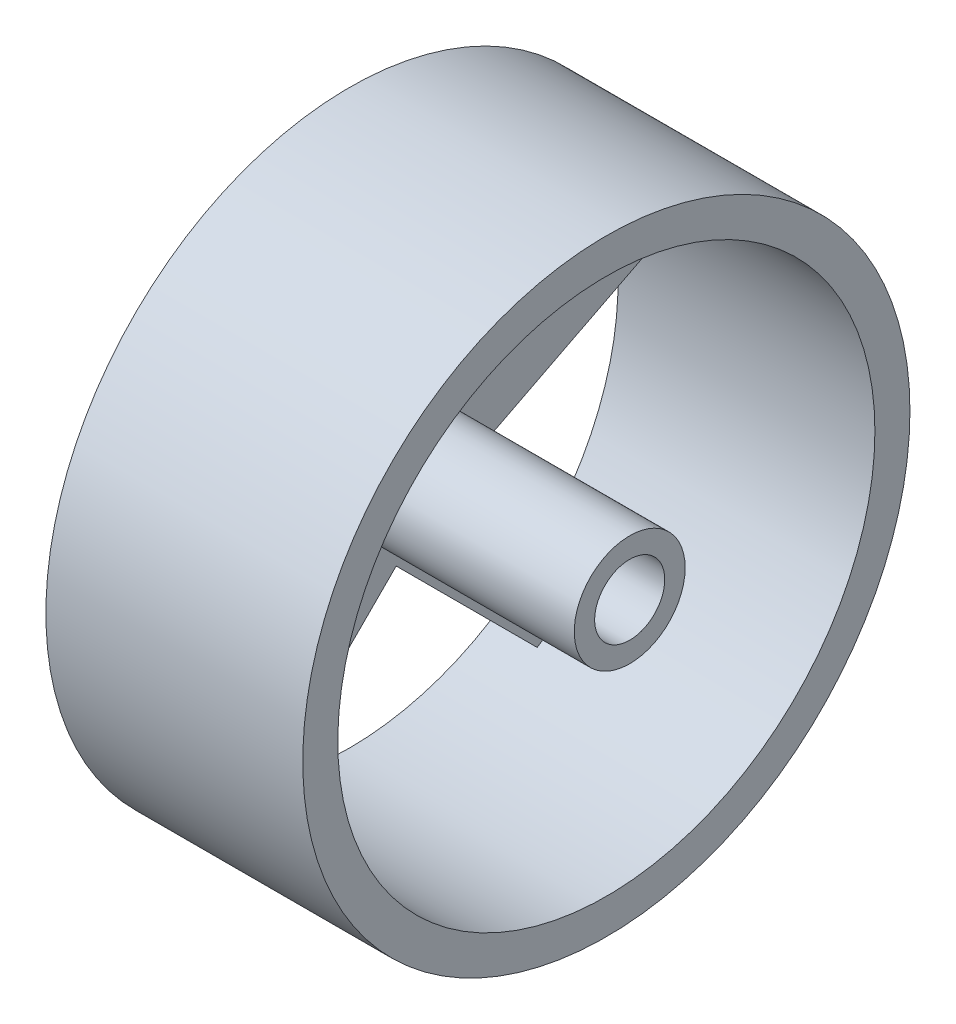
SolidWorks part; units mm, degrees
ref_plane "前视基准面" through (0, 0, 0) normal (0, 0, 1) x (1, 0, 0)
ref_plane "上视基准面" through (0, 0, 0) normal (0, 1, 0) x (1, 0, 0)
ref_plane "右视基准面" through (0, 0, 0) normal (1, 0, 0) x (0, 0, -1)
other "Configuration Table"
sketch "草图1" plane through (0, 0, 0) normal (1, 0, 0) x (0, 0, -1)
  circle A0 centre (0, 0) radius 26
  dimension "D1" = 52
extrude "凸台-拉伸1" add sketch "草图1" along normal blind 4
sketch "草图2" plane through (4, 0, 0) normal (1, 0, 0) x (0, 0, -1)
  circle A0 centre (0, 0) radius 4.75
  dimension "D1" = 9.5
extrude "凸台-拉伸2" add sketch "草图2" along normal blind 20
sketch "草图3" plane through (24, 0, 0) normal (1, 0, 0) x (0, 0, -1)
  circle A0 centre (0, 0) radius 3
  dimension "D1" = 6
extrude "切除-拉伸1" cut sketch "草图3" against normal blind 20
sketch "草图4" plane through (4, 0, 0) normal (1, 0, 0) x (0, 0, -1)
  circle A0 centre (0, 0) radius 23
  circle A1 centre (0, 0) radius 26 construction
  circle A2 centre (0, 0) radius 26
  dimension "D1" = 3
extrude "凸台-拉伸3" add sketch "草图4" along normal blind 18
sketch "草图5" plane through (4, 0, 0) normal (1, 0, 0) x (0, 0, -1)
  line L0 (0, 0) -> (-13.5191, 18.6074) construction
  line L1 (-21.2751, 8.739) -> (-4.4084, 6.0676)
  line L2 (-1.737, 22.9343) -> (-4.4084, 6.0676)
  line L3 (21.2751, 8.739) -> (4.4084, 6.0676)
  line L4 (1.737, 22.9343) -> (4.4084, 6.0676)
  line L5 (14.8857, -17.5333) -> (7.1329, -2.3176)
  line L6 (22.3486, 5.4351) -> (7.1329, -2.3176)
  line L7 (-12.0752, -19.5752) -> (0, -7.5)
  line L8 (12.0752, -19.5752) -> (0, -7.5)
  line L9 (-22.3486, 5.4351) -> (-7.1329, -2.3176)
  line L10 (-14.8857, -17.5333) -> (-7.1329, -2.3176)
  line L11 (0, 0) -> (0, 27.4185) construction
  arc A0 (-1.737, 22.9343) -> (-21.2751, 8.739) centre (0, 0) ccw
  circle A1 centre (0, 0) radius 23 construction
  arc A2 (21.2751, 8.739) -> (1.737, 22.9343) centre (0, 0) ccw
  arc A3 (14.8857, -17.5333) -> (22.3486, 5.4351) centre (0, 0) ccw
  arc A4 (-12.0752, -19.5752) -> (12.0752, -19.5752) centre (0, 0) ccw
  arc A5 (-22.3486, 5.4351) -> (-14.8857, -17.5333) centre (0, 0) ccw
  point P6 (-4.4324, 6.085)
  point P23 (0, 0)
  point P24 (0, 0)
  dimension "D2" = 7.5
  dimension "D3" = 90
  dimension "D4" = 3.4739
  dimension "D1" = 5
extrude "切除-拉伸2" cut sketch "草图5" against normal through all
sketch "草图6" plane through (0, 0, 0) normal (-1, 0, 0) x (0, 0, 1)
  circle A0 centre (0, 0) radius 5
  dimension "D1" = 10
extrude "切除-拉伸3" cut sketch "草图6" against normal blind 2
sketch "草图7" plane through (2, 0, 0) normal (-1, 0, 0) x (0, 0, 1)
  circle A0 centre (0, 0) radius 2.5
  dimension "D1" = 5
extrude "凸台-拉伸4" add sketch "草图7" along normal blind 3
